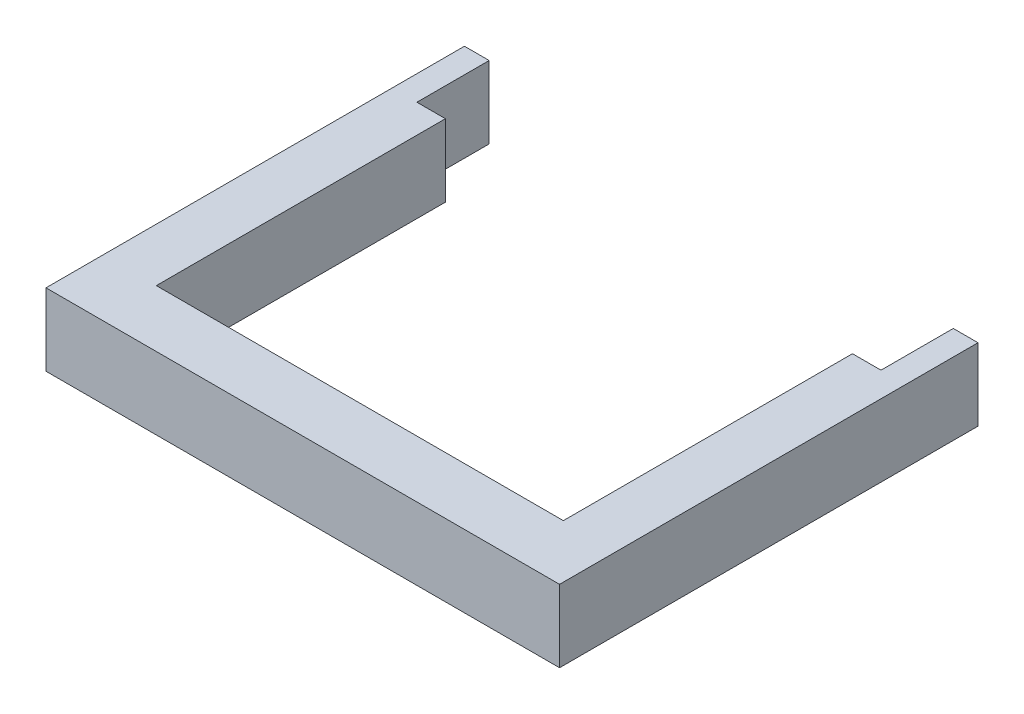
SolidWorks part; units mm, degrees
ref_plane "Front Plane" through (0, 0, 0) normal (0, 0, 1) x (1, 0, 0)
ref_plane "Top Plane" through (0, 0, 0) normal (0, 1, 0) x (1, 0, 0)
ref_plane "Right Plane" through (0, 0, 0) normal (1, 0, 0) x (0, 0, -1)
sketch "Sketch1" plane through (0, 0, 0) normal (0, 1, 0) x (1, 0, 0)
  line L0 (-13.5, 0) -> (13.5, 0)
  line L1 (13.5, 0) -> (13.5, 22)
  line L2 (13.5, 22) -> (12.2, 22)
  line L3 (12.2, 22) -> (12.2, 18.2)
  line L4 (12.2, 18.2) -> (10.7, 18.2)
  line L5 (10.7, 18.2) -> (10.7, 3)
  line L6 (10.7, 3) -> (-10.7, 3)
  line L7 (0, 3) -> (0, 0) construction
  line L8 (-10.7, 18.2) -> (-10.7, 3)
  line L9 (-12.2, 18.2) -> (-10.7, 18.2)
  line L10 (-12.2, 22) -> (-12.2, 18.2)
  line L11 (-13.5, 22) -> (-12.2, 22)
  line L12 (-13.5, 0) -> (-13.5, 22)
  dimension "D1" = 1.3
  dimension "D2" = 1.5
  dimension "D3" = 22
  dimension "D4" = 3
  dimension "D5" = 3.8
  dimension "D6" = 13.5
extrude "Boss-Extrude1" add sketch "Sketch1" along normal blind 3.8
